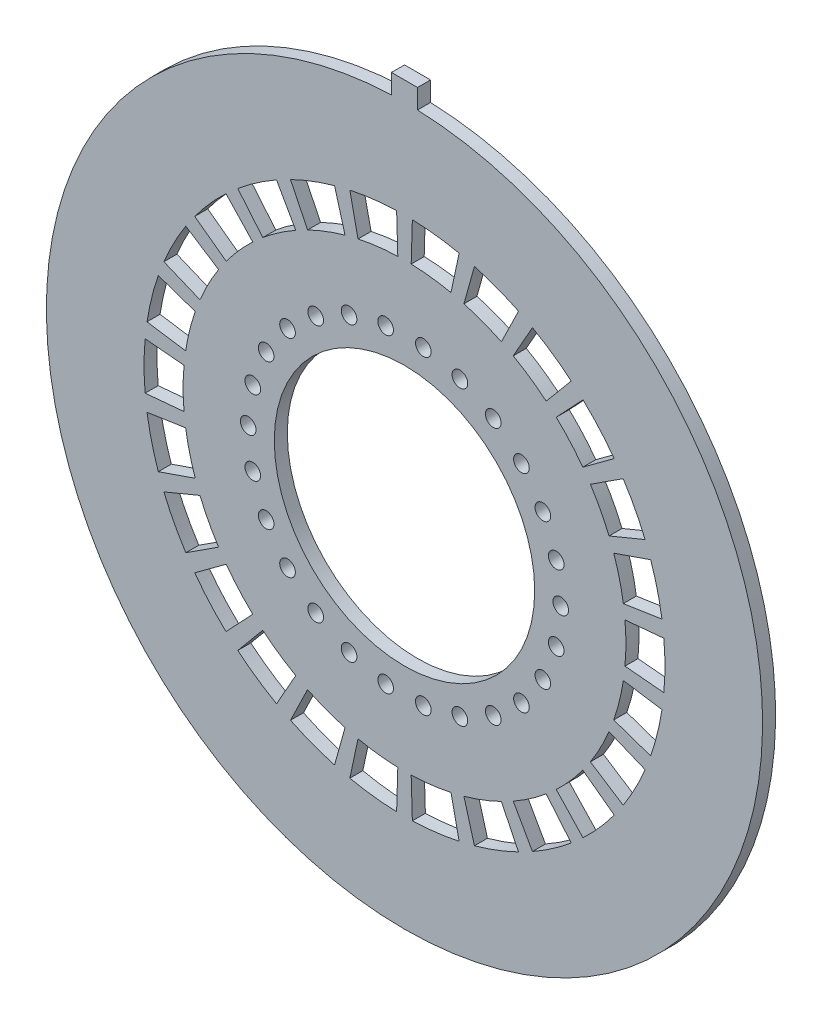
SolidWorks part; units mm, degrees
material "ABS"
ref_plane "Front Plane" through (0, 0, 0) normal (0, 0, 1) x (1, 0, 0)
ref_plane "Top Plane" through (0, 0, 0) normal (0, 1, 0) x (1, 0, 0)
ref_plane "Right Plane" through (0, 0, 0) normal (1, 0, 0) x (0, 0, -1)
sketch "PCB dimension" plane through (0, 0, 0) normal (0, 0, 1) x (1, 0, 0)
  line L0 (0, 0) -> (0, 42.7396) construction
  line L1 (-1, 27.4818) -> (-1, 28.9818)
  line L2 (-1, 28.9818) -> (1, 28.9818)
  line L3 (1, 28.9818) -> (1, 27.4818)
  line L4 (0, 0) -> (40.2767, 0) construction
  line L5 (0, 0) -> (37.5544, 0) construction
  arc A0 (-1, 27.4818) -> (1, 27.4818) centre (0, 0) ccw
  circle A1 centre (12, 0) radius 0.6
  circle A2 centre (11.6513, -2.8718) radius 0.6
  circle A3 centre (10.6255, -5.5767) radius 0.6
  circle A4 centre (8.9821, -7.9575) radius 0.6
  circle A5 centre (6.8168, -9.8758) radius 0.6
  circle A6 centre (4.2553, -11.2202) radius 0.6
  circle A7 centre (1.4464, -11.9125) radius 0.6
  circle A8 centre (-1.4464, -11.9125) radius 0.6
  circle A9 centre (-4.2553, -11.2202) radius 0.6
  circle A10 centre (-6.8168, -9.8758) radius 0.6
  circle A11 centre (-8.9821, -7.9575) radius 0.6
  circle A12 centre (-10.6255, -5.5767) radius 0.6
  circle A13 centre (-11.6513, -2.8718) radius 0.6
  circle A14 centre (-12, 0) radius 0.6
  circle A15 centre (-11.6513, 2.8718) radius 0.6
  circle A16 centre (-10.6255, 5.5767) radius 0.6
  circle A17 centre (-8.9821, 7.9575) radius 0.6
  circle A18 centre (-6.8168, 9.8758) radius 0.6
  circle A19 centre (-4.2553, 11.2202) radius 0.6
  circle A20 centre (-1.4464, 11.9125) radius 0.6
  circle A21 centre (1.4464, 11.9125) radius 0.6
  circle A22 centre (4.2553, 11.2202) radius 0.6
  circle A23 centre (6.8168, 9.8758) radius 0.6
  circle A24 centre (8.9821, 7.9575) radius 0.6
  circle A25 centre (10.6255, 5.5767) radius 0.6
  circle A26 centre (11.6513, 2.8718) radius 0.6
  circle A27 centre (0, 0) radius 10
  point P6 (0, 28.9818)
  point P64 (0, 0)
  dimension "D1" = 55
  dimension "D5" = 1.2
  dimension "D8" = 20
  dimension "D2" = 1.5
  dimension "D3" = 2
  dimension "D4" = 0
  dimension "D6" = 12
  dimension "D7" = 26
extrude "Boss-Extrude1" add sketch "PCB dimension" along normal blind 1
sketch "Sketch1" plane through (0, 0, 1) normal (0, 0, 1) x (1, 0, 0)
  line L0 (0, 0) -> (33.8166, 0) construction
  line L1 (0, 0) -> (34.0149, 4.1302) construction
  line L2 (0, 0) -> (34.1307, -4.1442) construction
  line L3 (0, 0) -> (33.9403, 3.0842) construction
  line L4 (0, 0) -> (33.2443, -3.021) construction
  line L5 (16.9302, 1.5385) -> (19.9179, 1.81)
  line L6 (19.9179, -1.81) -> (16.9302, -1.5385)
  line L7 (18.906, -6.5241) -> (16.0701, -5.5454)
  line L8 (16.8065, -2.5579) -> (19.7723, -3.0093)
  line L9 (16.7953, -10.859) -> (14.276, -9.2301)
  line L10 (15.706, -6.5056) -> (18.4776, -7.6537)
  line L11 (13.7085, -14.5628) -> (11.6523, -12.3784)
  line L12 (13.6927, -10.0753) -> (16.109, -11.8532)
  line L13 (9.8251, -17.4203) -> (8.3513, -14.8073)
  line L14 (10.8836, -13.0594) -> (12.8043, -15.364)
  line L15 (5.3706, -19.2654) -> (4.565, -16.3756)
  line L16 (7.4421, -15.2845) -> (8.7554, -17.9818)
  line L17 (0.6041, -19.9909) -> (0.5135, -16.9922)
  line L18 (3.568, -16.6214) -> (4.1976, -19.5545)
  line L19 (-4.1976, -19.5545) -> (-3.568, -16.6214)
  line L20 (-0.5135, -16.9922) -> (-0.6041, -19.9909)
  line L21 (-8.7554, -17.9818) -> (-7.4421, -15.2845)
  line L22 (-4.565, -16.3756) -> (-5.3706, -19.2654)
  line L23 (-12.8043, -15.364) -> (-10.8836, -13.0594)
  line L24 (-8.3513, -14.8073) -> (-9.8251, -17.4203)
  line L25 (-16.109, -11.8532) -> (-13.6927, -10.0753)
  line L26 (-11.6523, -12.3784) -> (-13.7085, -14.5628)
  line L27 (-18.4776, -7.6537) -> (-15.706, -6.5056)
  line L28 (-14.276, -9.2301) -> (-16.7953, -10.859)
  line L29 (-19.7723, -3.0093) -> (-16.8065, -2.5579)
  line L30 (-16.0701, -5.5454) -> (-18.906, -6.5241)
  line L31 (-19.9179, 1.81) -> (-16.9302, 1.5385)
  line L32 (-16.9302, -1.5385) -> (-19.9179, -1.81)
  line L33 (-18.906, 6.5241) -> (-16.0701, 5.5454)
  line L34 (-16.8065, 2.5579) -> (-19.7723, 3.0093)
  line L35 (-16.7953, 10.859) -> (-14.276, 9.2301)
  line L36 (-15.706, 6.5056) -> (-18.4776, 7.6537)
  line L37 (-13.7085, 14.5628) -> (-11.6523, 12.3784)
  line L38 (-13.6927, 10.0753) -> (-16.109, 11.8532)
  line L39 (-9.8251, 17.4203) -> (-8.3513, 14.8073)
  line L40 (-10.8836, 13.0594) -> (-12.8043, 15.364)
  line L41 (-5.3706, 19.2654) -> (-4.565, 16.3756)
  line L42 (-7.4421, 15.2845) -> (-8.7554, 17.9818)
  line L43 (-0.6041, 19.9909) -> (-0.5135, 16.9922)
  line L44 (-3.568, 16.6214) -> (-4.1976, 19.5545)
  line L45 (4.1976, 19.5545) -> (3.568, 16.6214)
  line L46 (0.5135, 16.9922) -> (0.6041, 19.9909)
  line L47 (8.7554, 17.9818) -> (7.4421, 15.2845)
  line L48 (4.565, 16.3756) -> (5.3706, 19.2654)
  line L49 (12.8043, 15.364) -> (10.8836, 13.0594)
  line L50 (8.3513, 14.8073) -> (9.8251, 17.4203)
  line L51 (16.109, 11.8532) -> (13.6927, 10.0753)
  line L52 (11.6523, 12.3784) -> (13.7085, 14.5628)
  line L53 (18.4776, 7.6537) -> (15.706, 6.5056)
  line L54 (14.276, 9.2301) -> (16.7953, 10.859)
  line L55 (19.7723, 3.0093) -> (16.8065, 2.5579)
  line L56 (16.0701, 5.5454) -> (18.906, 6.5241)
  arc A0 (19.9179, -1.81) -> (19.9179, 1.81) centre (0, 0) ccw
  arc A1 (16.9302, -1.5385) -> (16.9302, 1.5385) centre (0, 0) ccw
  arc A2 (16.0701, -5.5454) -> (16.8065, -2.5579) centre (0, 0) ccw
  arc A3 (18.906, -6.5241) -> (19.7723, -3.0093) centre (0, 0) ccw
  arc A4 (14.276, -9.2301) -> (15.706, -6.5056) centre (0, 0) ccw
  arc A5 (16.7953, -10.859) -> (18.4776, -7.6537) centre (0, 0) ccw
  arc A6 (11.6523, -12.3784) -> (13.6927, -10.0753) centre (0, 0) ccw
  arc A7 (13.7085, -14.5628) -> (16.109, -11.8532) centre (0, 0) ccw
  arc A8 (8.3513, -14.8073) -> (10.8836, -13.0594) centre (0, 0) ccw
  arc A9 (9.8251, -17.4203) -> (12.8043, -15.364) centre (0, 0) ccw
  arc A10 (4.565, -16.3756) -> (7.4421, -15.2845) centre (0, 0) ccw
  arc A11 (5.3706, -19.2654) -> (8.7554, -17.9818) centre (0, 0) ccw
  arc A12 (0.5135, -16.9922) -> (3.568, -16.6214) centre (0, 0) ccw
  arc A13 (0.6041, -19.9909) -> (4.1976, -19.5545) centre (0, 0) ccw
  arc A14 (-3.568, -16.6214) -> (-0.5135, -16.9922) centre (0, 0) ccw
  arc A15 (-4.1976, -19.5545) -> (-0.6041, -19.9909) centre (0, 0) ccw
  arc A16 (-7.4421, -15.2845) -> (-4.565, -16.3756) centre (0, 0) ccw
  arc A17 (-8.7554, -17.9818) -> (-5.3706, -19.2654) centre (0, 0) ccw
  arc A18 (-10.8836, -13.0594) -> (-8.3513, -14.8073) centre (0, 0) ccw
  arc A19 (-12.8043, -15.364) -> (-9.8251, -17.4203) centre (0, 0) ccw
  arc A20 (-13.6927, -10.0753) -> (-11.6523, -12.3784) centre (0, 0) ccw
  arc A21 (-16.109, -11.8532) -> (-13.7085, -14.5628) centre (0, 0) ccw
  arc A22 (-15.706, -6.5056) -> (-14.276, -9.2301) centre (0, 0) ccw
  arc A23 (-18.4776, -7.6537) -> (-16.7953, -10.859) centre (0, 0) ccw
  arc A24 (-16.8065, -2.5579) -> (-16.0701, -5.5454) centre (0, 0) ccw
  arc A25 (-19.7723, -3.0093) -> (-18.906, -6.5241) centre (0, 0) ccw
  arc A26 (-16.9302, 1.5385) -> (-16.9302, -1.5385) centre (0, 0) ccw
  arc A27 (-19.9179, 1.81) -> (-19.9179, -1.81) centre (0, 0) ccw
  arc A28 (-16.0701, 5.5454) -> (-16.8065, 2.5579) centre (0, 0) ccw
  arc A29 (-18.906, 6.5241) -> (-19.7723, 3.0093) centre (0, 0) ccw
  arc A30 (-14.276, 9.2301) -> (-15.706, 6.5056) centre (0, 0) ccw
  arc A31 (-16.7953, 10.859) -> (-18.4776, 7.6537) centre (0, 0) ccw
  arc A32 (-11.6523, 12.3784) -> (-13.6927, 10.0753) centre (0, 0) ccw
  arc A33 (-13.7085, 14.5628) -> (-16.109, 11.8532) centre (0, 0) ccw
  arc A34 (-8.3513, 14.8073) -> (-10.8836, 13.0594) centre (0, 0) ccw
  arc A35 (-9.8251, 17.4203) -> (-12.8043, 15.364) centre (0, 0) ccw
  arc A36 (-4.565, 16.3756) -> (-7.4421, 15.2845) centre (0, 0) ccw
  arc A37 (-5.3706, 19.2654) -> (-8.7554, 17.9818) centre (0, 0) ccw
  arc A38 (-0.5135, 16.9922) -> (-3.568, 16.6214) centre (0, 0) ccw
  arc A39 (-0.6041, 19.9909) -> (-4.1976, 19.5545) centre (0, 0) ccw
  arc A40 (3.568, 16.6214) -> (0.5135, 16.9922) centre (0, 0) ccw
  arc A41 (4.1976, 19.5545) -> (0.6041, 19.9909) centre (0, 0) ccw
  arc A42 (7.4421, 15.2845) -> (4.565, 16.3756) centre (0, 0) ccw
  arc A43 (8.7554, 17.9818) -> (5.3706, 19.2654) centre (0, 0) ccw
  arc A44 (10.8836, 13.0594) -> (8.3513, 14.8073) centre (0, 0) ccw
  arc A45 (12.8043, 15.364) -> (9.8251, 17.4203) centre (0, 0) ccw
  arc A46 (13.6927, 10.0753) -> (11.6523, 12.3784) centre (0, 0) ccw
  arc A47 (16.109, 11.8532) -> (13.7085, 14.5628) centre (0, 0) ccw
  arc A48 (15.706, 6.5056) -> (14.276, 9.2301) centre (0, 0) ccw
  arc A49 (18.4776, 7.6537) -> (16.7953, 10.859) centre (0, 0) ccw
  arc A50 (16.8065, 2.5579) -> (16.0701, 5.5454) centre (0, 0) ccw
  arc A51 (19.7723, 3.0093) -> (18.906, 6.5241) centre (0, 0) ccw
  point P113 (0, 0)
  dimension "D1" = 40
  dimension "D2" = 3
  dimension "D3" = 6.923
  dimension "D4" = 6.923
  dimension "D5" = 5.192
  dimension "D6" = 5.192
  dimension "D7" = 26
extrude "Cut-Extrude1" cut sketch "Sketch1" against normal through all
